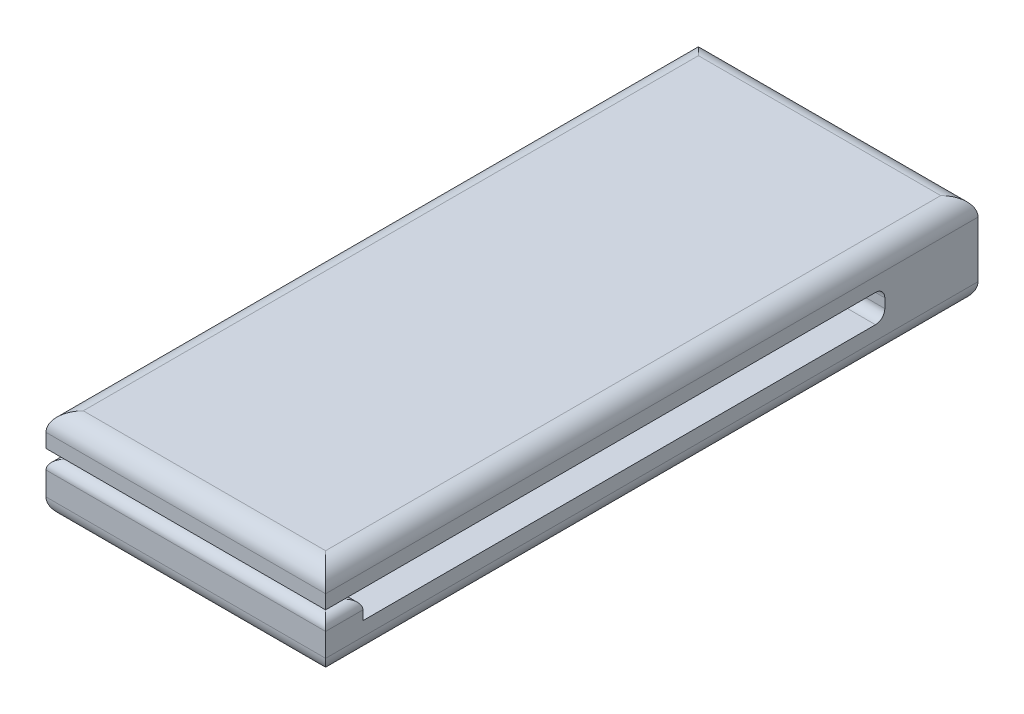
SolidWorks part; units mm, degrees
ref_plane "Front Plane" through (0, 0, 0) normal (0, 0, 1) x (1, 0, 0)
ref_plane "Top Plane" through (0, 0, 0) normal (0, 1, 0) x (1, 0, 0)
ref_plane "Right Plane" through (0, 0, 0) normal (1, 0, 0) x (0, 0, -1)
sketch "Sketch1" plane through (0, 0, 0) normal (0, 1, 0) x (1, 0, 0)
  line L1 (-7.5, -17.5) -> (7.5, -17.5)
  line L2 (-7.5, -17.5) -> (-7.5, 17.5)
  line L3 (-7.5, 17.5) -> (7.5, 17.5)
  line L4 (7.5, -17.5) -> (7.5, 17.5)
  line L5 (-7.5, -17.5) -> (7.5, 17.5) construction
  line L6 (-7.5, 17.5) -> (7.5, -17.5) construction
  point P0 (0, 0)
  dimension "D1" = 15
  dimension "D2" = 35
extrude "Boss-Extrude1" add sketch "Sketch1" along normal blind 5
sketch "Sketch3" plane through (0, 0, 17.5) normal (0, 0, 1) x (1, 0, 0)
  line L0 (-7.5, 0) -> (-7.5, 1.75)
  line L1 (-7.5, 5) -> (-7.5, 0) construction
  line L2 (-7.5, 5) -> (-7.5, 3.25)
  dimension "D1" = 1.75
  dimension "D2" = 1.75
sketch "Sketch4" plane through (0, 0, 17.5) normal (0, 0, 1) x (1, 0, 0)
  line L0 (-7.5, 1.75) -> (-7.5, 3.25)
  line L1 (-7.5, 3.25) -> (7.5, 3.25)
  line L2 (7.5, 5) -> (7.5, 0) construction
  line L3 (7.5, 3.25) -> (7.5, 1.75)
  line L4 (7.5, 1.75) -> (-7.5, 1.75)
extrude "Cut-Extrude1" cut sketch "Sketch4" against normal blind 30
fillet "Fillet1" radius 1 4 edges at (0, 5, 17.5) (-7.5, 5, 0) (0, 5, -17.5) (7.5, 5, 0)
fillet "Fillet2" radius 1 4 edges at (0, 0, -17.5) (-7.5, 0, 0) (0, 0, 17.5) (7.5, 0, 0)
fillet "Fillet3" radius 0.5 1 edges at (0, 3.25, -12.5)
fillet "Fillet4" radius 0.5 1 edges at (0, 1.75, -12.5)
sketch "Sketch5" plane through (0, 1.75, 0) normal (0, 1, 0) x (1, 0, 0)
  line L0 (7.5, 12) -> (7.5, -17.5) construction
  line L1 (-7.5, -17.5) -> (7.5, -17.5)
  line L2 (-7.5, -17.5) -> (-7.5, -15.5)
  line L3 (-7.5, -15.5) -> (7.5, -15.5)
  line L4 (7.5, -17.5) -> (7.5, -15.5)
  dimension "D1" = 2
extrude "Boss-Extrude2" add sketch "Sketch5" along normal blind 1.5
sketch "Sketch6" plane through (7.5, 0, 0) normal (1, 0, 0) x (0, 0, -1)
  line L0 (-15.5, 3.25) -> (-15.5, 2.75)
  line L1 (-15.5, 3.25) -> (-15.5, 1.75) construction
  dimension "D1" = 0.5
sketch "Sketch8" plane through (7.5, 0, 0) normal (1, 0, 0) x (0, 0, -1)
  line L0 (-15.5, 2.75) -> (-17.5, 2.75)
  line L1 (-17.5, 4) -> (-17.5, 1) construction
  line L2 (-15.5, 3.25) -> (-17.5, 3.25)
  line L3 (-17.5, 3.25) -> (-17.5, 2.75)
  line L4 (-15.5, 3.25) -> (-15.5, 2.75)
extrude "Cut-Extrude3" cut sketch "Sketch8" against normal blind 15
fillet "Fillet5" radius 0.5 4 edges at (0, 2.75, 17.5) (-7.5, 2.75, 16.5) (0, 2.75, 15.5) (7.5, 2.75, 16.5)
